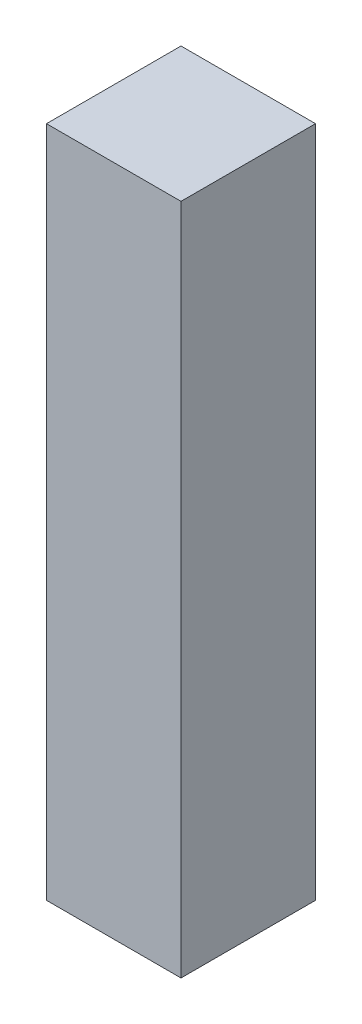
SolidWorks part; units mm, degrees
ref_plane "Front Plane" through (0, 0, 0) normal (0, 0, 1) x (1, 0, 0)
ref_plane "Top Plane" through (0, 0, 0) normal (0, 1, 0) x (1, 0, 0)
ref_plane "Right Plane" through (0, 0, 0) normal (1, 0, 0) x (0, 0, -1)
sketch "Sketch1" plane through (0, 0, 0) normal (0, 1, 0) x (1, 0, 0)
  line L0 (-10.2, 8.55) -> (-10.2, -11.45)
  line L1 (-10.2, 8.55) -> (9.8, 8.55)
  line L2 (9.8, 8.55) -> (9.8, -11.45)
  line L3 (-10.2, -11.45) -> (9.8, -11.45)
  dimension "D1" = 20
  dimension "D2" = 20
  dimension "D3" = 20
  dimension "D4" = 20
extrude "Boss-Extrude1" add sketch "Sketch1" along normal blind 100
